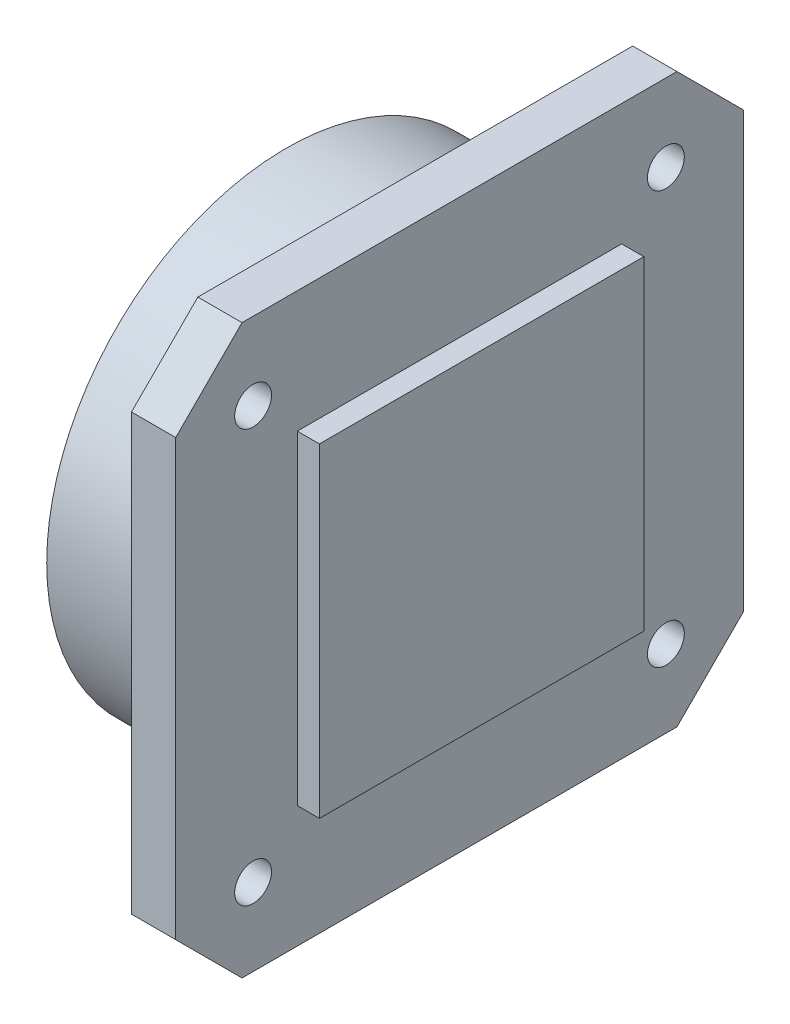
SolidWorks part; units mm, degrees
ref_plane "Front Plane" through (0, 0, 0) normal (0, 0, 1) x (1, 0, 0)
ref_plane "Top Plane" through (0, 0, 0) normal (0, 1, 0) x (1, 0, 0)
ref_plane "Right Plane" through (0, 0, 0) normal (1, 0, 0) x (0, 0, -1)
sketch "Sketch1" plane through (0, 0, 0) normal (1, 0, 0) x (0, 0, -1)
  line L0 (0, 68) -> (9, 77)
  line L1 (9, 0) -> (68, 0)
  line L2 (0, 9) -> (0, 68)
  line L3 (9, 77) -> (68, 77)
  line L4 (77, 9) -> (77, 68)
  line L5 (68, 77) -> (77, 68)
  line L6 (0, 9) -> (9, 0)
  line L7 (68, 0) -> (77, 9)
  dimension "D3" = 59
  dimension "D4" = 59
  dimension "D5" = 59
  dimension "D6" = 59
  dimension "D7" = 9
  dimension "D9" = 9
  dimension "D10" = 9
extrude "Extrude1" add sketch "Sketch1" along normal blind 6
sketch "Sketch2" plane through (6, 0, 0) normal (1, 0, 0) x (0, 0, -1)
  line L0 (0, 68) -> (0, 9) construction
  line L1 (16.5, 60.5) -> (60.5, 60.5)
  line L2 (16.5, 60.5) -> (16.5, 16.5)
  line L3 (16.5, 16.5) -> (60.5, 16.5)
  line L4 (60.5, 60.5) -> (60.5, 16.5)
  line L5 (68, 77) -> (9, 77) construction
  dimension "D1" = 44
  dimension "D2" = 44
  dimension "D3" = 16.5
  dimension "D4" = 16.5
extrude "Extrude2" add sketch "Sketch2" along normal blind 3
sketch "Sketch3" plane through (9, 0, 0) normal (1, 0, 0) x (0, 0, -1)
  line L0 (60.5, 60.5) -> (16.5, 60.5) construction
  line L1 (16.5, 60.5) -> (16.5, 16.5) construction
  circle A0 centre (38.5, 38.5) radius 9
  dimension "D3" = 18
  dimension "D1" = 22
  dimension "D2" = 22
sketch "Sketch4" plane through (0, 0, 0) normal (-1, 0, 0) x (0, 0, 1)
  circle A0 centre (-38.5, 38.5) radius 32.5
  dimension "D1" = 65
extrude "Extrude3" add sketch "Sketch4" along normal blind 17.5
extrude "Extrude4" [suppressed] cut sketch "Sketch3" against normal through all
sketch3d "3DSketch1" plane through (0, 0, 0) normal (0, 0, 1) x (1, 0, 0)
  dimension "D1" = 38.5
sketch "Sketch13" plane through (0, 38.5, 0) normal (0, -1, 0) x (1, 0, 0)
  line L0 (9, -38.5) -> (-17.5, -38.5) construction
  line L1 (9, -16.5) -> (9, -60.5) construction
  line L2 (-17.5, -6) -> (-17.5, -71) construction
sketch "Sketch16" plane through (-17.5, 0, 0) normal (-1, 0, 0) x (0, 0, 1)
  line L0 (-17.875, 38.5) -> (17.875, 38.5) construction
  circle A0 centre (-38.5, 38.5) radius 21
  circle A1 centre (-38.5, 38.5) radius 32.5 construction
  dimension "D2" = 42
  dimension "D3" = 0
  dimension "D1" = 0
extrude "Extrude7" cut sketch "Sketch16" against normal blind 12
sketch "Sketch18" plane through (0, 38.5, 0) normal (0, -1, 0) x (1, 0, 0)
  line L0 (-5.5, -56.5) -> (-5.5, -59.5)
  line L1 (-5.5, -17.5) -> (-5.5, -59.5) construction
  line L2 (-5.5, -59.5) -> (-17.5, -59.5)
  line L3 (-17.5, -6) -> (-17.5, -71) construction
  line L4 (-17.5, -59.5) -> (-5.5, -56.5)
  dimension "D1" = 3
revolve "Revolve2" add sketch "Sketch18" angle 360 about L0
sketch "Sketch19" plane through (6, 0, 0) normal (1, 0, 0) x (0, 0, -1)
  line L0 (68, 77) -> (9, 77) construction
  line L1 (0, 68) -> (0, 9) construction
  circle A0 centre (10.5, 66.5) radius 2.5
  dimension "D3" = 5
  dimension "D1" = 10.5
  dimension "D2" = 10.5
extrude "Extrude8" cut sketch "Sketch19" against normal through all
pattern_linear "LPattern1" count 2 spacing 56 along (0, 0, -1) of "Extrude8"
pattern_linear "LPattern2" count 2 spacing 56 along (0, -1, 0) of "LPattern1", "Extrude8"
sketch "Sketch20" plane through (-5.5, 0, 0) normal (-1, 0, 0) x (0, 0, 1)
  circle A0 centre (-38.5, 38.5) radius 12.5
  dimension "D1" = 25
extrude "Extrude10" cut sketch "Sketch20" against normal blind 4
